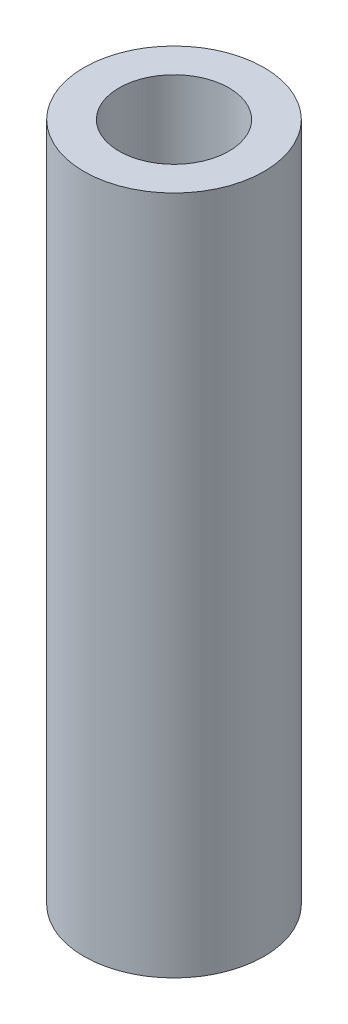
SolidWorks part; units mm, degrees
ref_plane "Front Plane" through (0, 0, 0) normal (0, 0, 1) x (1, 0, 0)
ref_plane "Top Plane" through (0, 0, 0) normal (0, 1, 0) x (1, 0, 0)
ref_plane "Right Plane" through (0, 0, 0) normal (1, 0, 0) x (0, 0, -1)
sketch "Sketch1" plane through (0, 0, 0) normal (0, 1, 0) x (1, 0, 0)
  circle A3 centre (59.4755, 35.57) radius 4.1
extrude "Boss-Extrude1" add sketch "Sketch1" against normal blind 30.95
hole_wizard "Tap Drill for M6 Tap1" positions "Sketch2" profile "Sketch3" hole size "M6" standard "ISO" end condition through all
sketch "Sketch2" plane through (0, -30.95, 0) normal (0, -1, 0) x (-1, 0, 0)
  point P0 (-59.4755, 35.57)
sketch "Sketch3" plane through (59.4755, -30.95, -35.57) normal (1, 0, 0) x (0, 0, -1)
  line L0 (0, 0) -> (0, 30.95)
  line L1 (0, 30.95) -> (2.5, 30.95)
  line L2 (2.5, 30.95) -> (2.5, 0)
  line L5 (2.5, 0) -> (0, 0)
  line L11 (0, -6.35) -> (0, 107.95) construction
  dimension "Thru Hole Dia." = 5
  dimension "Thru Hole Depth" = 30.95
